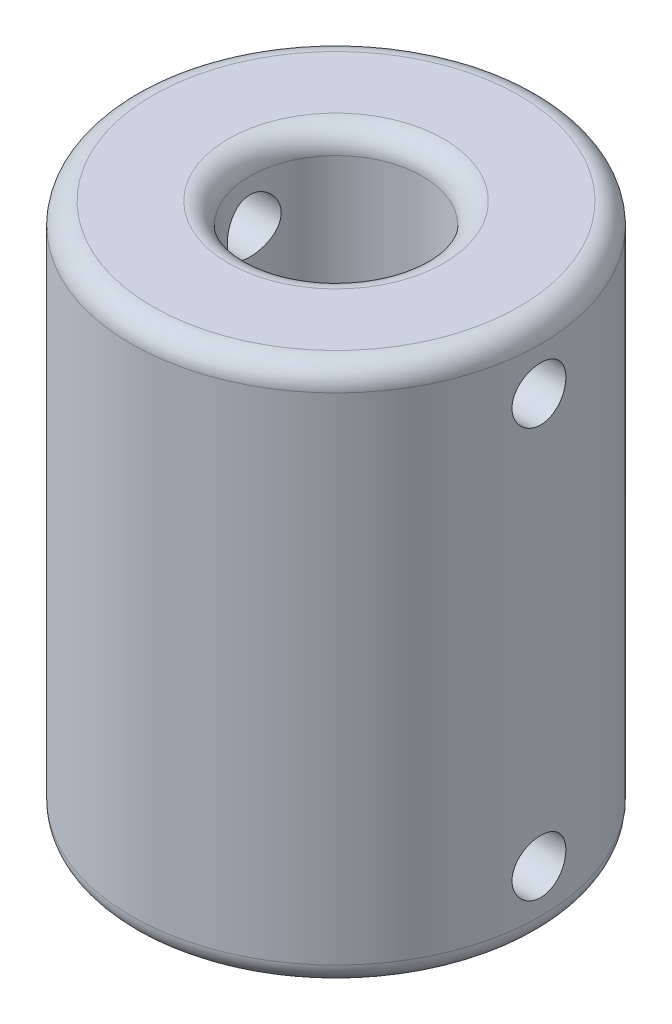
SolidWorks part; units mm, degrees
ref_plane "Front Plane" through (0, 0, 0) normal (0, 0, 1) x (1, 0, 0)
ref_plane "Top Plane" through (0, 0, 0) normal (0, 1, 0) x (1, 0, 0)
ref_plane "Right Plane" through (0, 0, 0) normal (1, 0, 0) x (0, 0, -1)
sketch "Sketch1" plane through (0, 0, 0) normal (0, 1, 0) x (1, 0, 0)
  circle A0 centre (0, 0) radius 2.5
  circle A1 centre (0, 0) radius 9.5
  dimension "D1" = 5
  dimension "D2" = 19
extrude "Boss-Extrude1" add sketch "Sketch1" along normal blind 25
sketch "Sketch2" plane through (0, 25, 0) normal (0, 1, 0) x (1, 0, 0)
  circle A0 centre (0, 0) radius 4
  dimension "D1" = 8
extrude "Cut-Extrude1" cut sketch "Sketch2" against normal blind 12.5
sketch "Sketch3" plane through (0, 0, 0) normal (1, 0, 0) x (0, 0, -1)
  line L0 (0, 25.6656) -> (0, -1.4284) construction
  line L1 (9.5, 25) -> (-9.5, 25) construction
  line L2 (-9.5, 0) -> (9.5, 0) construction
  circle A0 centre (0, 22) radius 1.5
  circle A1 centre (0, 3) radius 1.5
  point P7 (0, 0)
  point P10 (0, 0)
  dimension "D1" = 3
  dimension "D2" = 3
  dimension "D3" = 3
  dimension "D4" = 3
hole_wizard "Tap Drill for M3 Tap1" positions "Sketch8" profile "Sketch7" hole size "M3" standard "ISO"
sketch "Sketch8" plane through (0, 0, 0) normal (1, 0, 0) x (0, 0, -1)
  point P0 (0, 22)
  point P3 (0, 3)
sketch "Sketch7" plane through (0, 22, 0) normal (0, 1, 0) x (0, 0, 1)
  line L0 (0, 0) -> (0, 9.5)
  line L1 (0, 9.5) -> (1.25, 9.5)
  line L2 (1.25, 9.5) -> (1.25, 0.025)
  line L3 (1.25, 0.025) -> (1.275, 0)
  line L5 (1.275, 0) -> (0, 0)
  line L6 (-1.25, 0.025) -> (-1.275, 0) construction
  line L11 (0, -6.35) -> (0, 107.95) construction
  dimension "Thru Hole Dia." = 2.5
  dimension "Thru Hole Depth" = 9.5
  dimension "Near C'Sink Dia." = 2.55
  dimension "Near C'Sink Angle" = 90
fillet "Fillet1" radius 1 4 edges at (0, 0, 2.5) (0, 0, 9.5) (0, 25, 4) (0, 25, 9.5)
mirror "Mirror3" about plane through (0, 0, 0) normal (1, 0, 0) of "Tap Drill for M3 Tap1"
